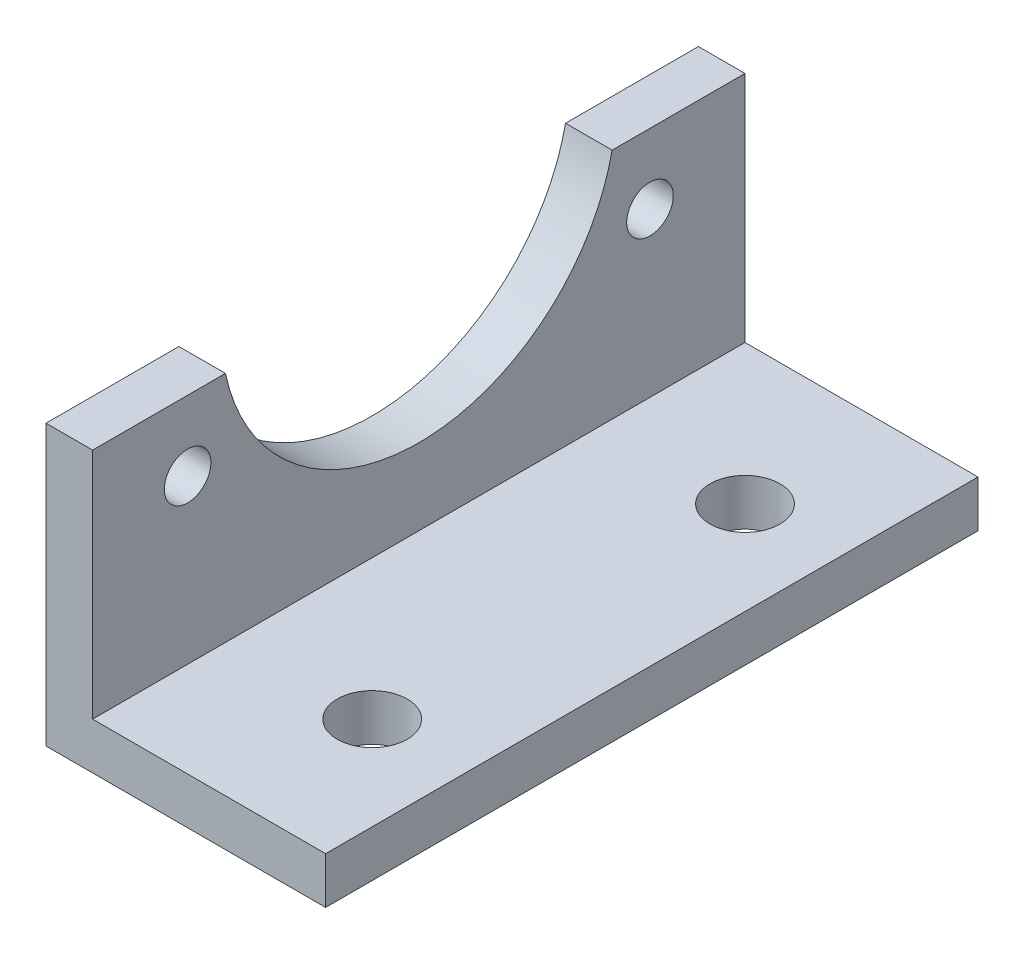
SolidWorks part; units mm, degrees
ref_plane "Front Plane" through (0, 0, 0) normal (0, 0, 1) x (1, 0, 0)
ref_plane "Top Plane" through (0, 0, 0) normal (0, 1, 0) x (1, 0, 0)
ref_plane "Right Plane" through (0, 0, 0) normal (1, 0, 0) x (0, 0, -1)
sketch "Sketch1" plane through (0, 0, 0) normal (0, 0, 1) x (1, 0, 0)
  line L0 (0, 0) -> (0, 38.1)
  line L1 (0, 38.1) -> (6.35, 38.1)
  line L2 (6.35, 38.1) -> (6.35, 6.35)
  line L3 (0, 0) -> (6.35, 6.35) construction
  line L4 (38.1, 6.35) -> (6.35, 6.35)
  line L5 (38.1, 0) -> (38.1, 6.35)
  line L6 (0, 0) -> (38.1, 0)
  dimension "D1" = 38.1
  dimension "D2" = 6.35
  dimension "D3" = 45
extrude "Boss-Extrude1" add sketch "Sketch1" along normal blind 88.9
sketch "Sketch2" plane through (0, 0, 0) normal (-1, 0, 0) x (0, 0, 1)
  line L0 (70.795, 38.1) -> (88.9, 38.1)
  line L1 (88.9, 38.1) -> (88.9, 0)
  line L2 (88.9, 0) -> (0, 0)
  line L3 (44.45, 0) -> (44.45, 16.7333) construction
  line L5 (0, 38.1) -> (0, 0)
  line L6 (18.105, 38.1) -> (0, 38.1)
  line L7 (18.105, 38.1) -> (70.795, 38.1)
  circle A0 centre (75.95, 28.575) radius 3.175
  circle A1 centre (12.95, 28.575) radius 3.175
  arc A3 (70.795, 38.1) -> (18.105, 38.1) centre (44.45, 43.6583) cw
  point P19 (75.95, 28.575)
  line M18 (88.9, 38.1) -> (0, 38.1)
  dimension "D1" = 6.35
  dimension "D2" = 38.1
  dimension "D5" = 26.925
  dimension "D3" = 44.45
  dimension "D4" = 9.525
  dimension "D6" = 88.9
extrude "Cut-Extrude1" cut sketch "Sketch2" against normal blind 76.2 contours A1 | A0 | A3 M18
sketch "Sketch3" plane through (0, 0, 0) normal (0, -1, 0) x (1, 0, 0)
  line L0 (0, 44.45) -> (25.4, 44.45) construction
  line L1 (0, 88.9) -> (0, 0) construction
  line L2 (25.4, 44.45) -> (25.4, 69.85) construction
  circle A0 centre (25.4, 69.85) radius 4.7625
  circle A1 centre (25.4, 19.05) radius 4.7625
  dimension "D3" = 9.525
  dimension "D1" = 25.4
  dimension "D2" = 25.4
extrude "Cut-Extrude2" cut sketch "Sketch3" against normal through all
